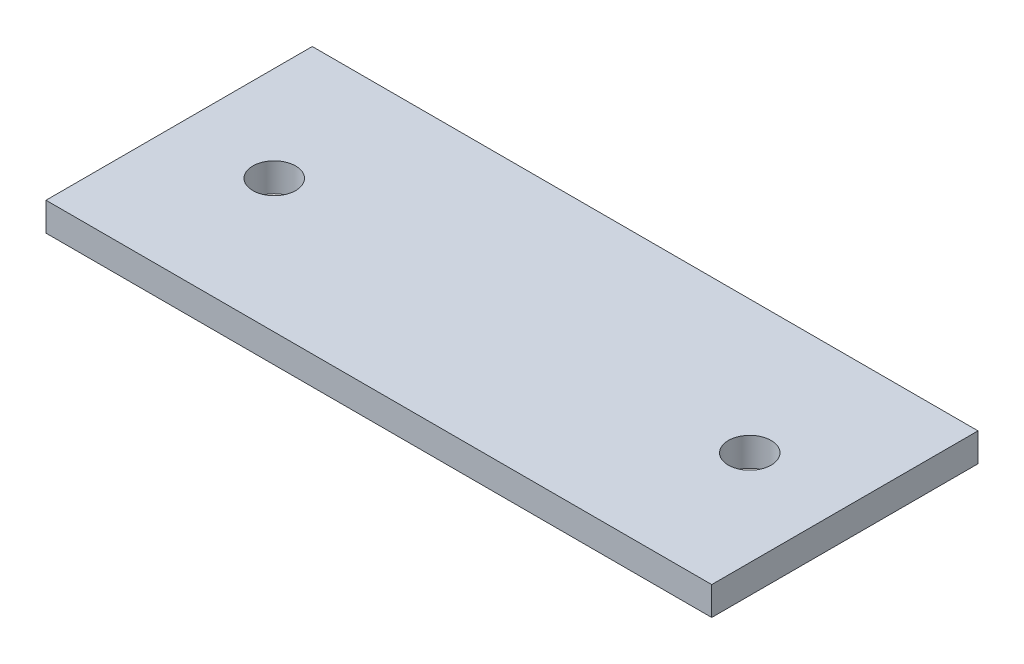
SolidWorks part; units mm, degrees
ref_plane "Front Plane" through (0, 0, 0) normal (0, 0, 1) x (1, 0, 0)
ref_plane "Top Plane" through (0, 0, 0) normal (0, 1, 0) x (1, 0, 0)
ref_plane "Right Plane" through (0, 0, 0) normal (1, 0, 0) x (0, 0, -1)
sketch "Sketch1" plane through (0, 0, 0) normal (0, 1, 0) x (1, 0, 0)
  line L0 (10, 28) -> (10, 0) construction
  line L1 (0, 0) -> (70, 0)
  line L2 (0, 0) -> (0, 28)
  line L3 (0, 28) -> (70, 28)
  line L4 (70, 0) -> (70, 28)
  line L5 (60, 28) -> (60, 0) construction
  circle A0 centre (10, 14) radius 2.25
  circle A1 centre (60, 14) radius 2.25
  dimension "D4" = 4.5
  dimension "D1" = 70
  dimension "D2" = 10
  dimension "D3" = 50
  dimension "D5" = 28
extrude "Boss-Extrude1" add sketch "Sketch1" along normal blind 3
